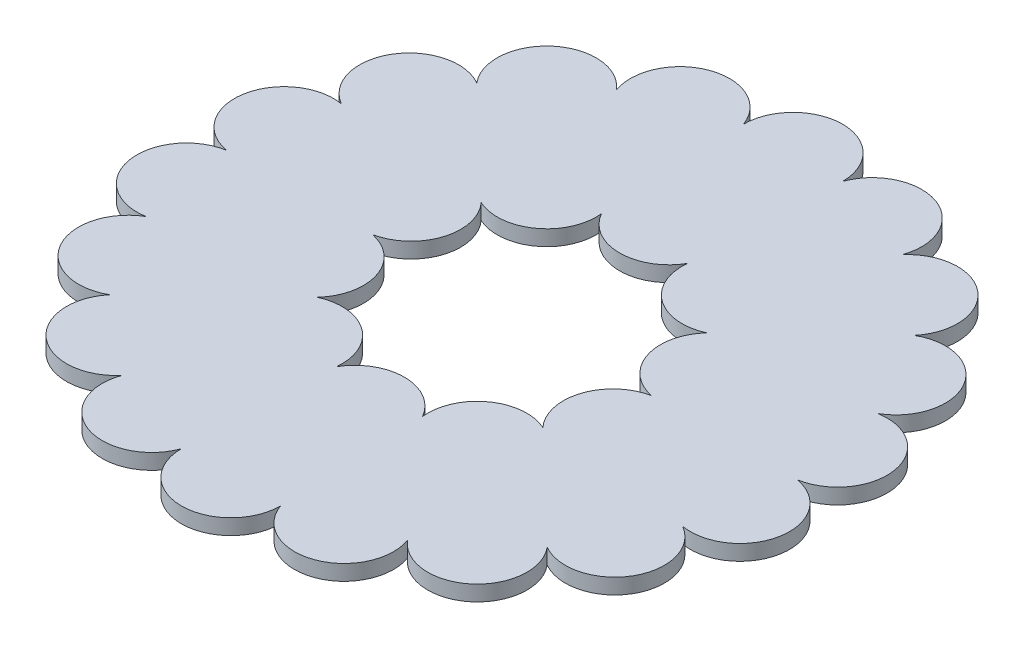
SolidWorks part; units mm, degrees
ref_plane "Front Plane" through (0, 0, 0) normal (0, 0, 1) x (1, 0, 0)
ref_plane "Top Plane" through (0, 0, 0) normal (0, 1, 0) x (1, 0, 0)
ref_plane "Right Plane" through (0, 0, 0) normal (1, 0, 0) x (0, 0, -1)
sketch "Sketch1" plane through (0, 0, 0) normal (0, 1, 0) x (1, 0, 0)
  circle A0 centre (0, 0) radius 64.4026
  circle A1 centre (0, 0) radius 115.2026
  point P8 (0, 0)
  dimension "D1" = 50.8
  dimension "D2" = 128.8051
extrude "Boss-Extrude1" add sketch "Sketch1" along normal blind 6.35
sketch "Sketch2" plane through (0, 6.35, 0) normal (0, 1, 0) x (1, 0, 0)
  circle A0 centre (0, 64.4026) radius 20.32
  circle A1 centre (0, 0) radius 64.4026 construction
  circle A2 centre (0, 115.2026) radius 20.32
  circle A3 centre (0, 0) radius 115.2026 construction
  circle A4 centre (37.8549, 52.1028) radius 20.32
  circle A5 centre (61.2505, 19.9015) radius 20.32
  circle A6 centre (61.2505, -19.9015) radius 20.32
  circle A7 centre (37.8549, -52.1028) radius 20.32
  circle A8 centre (0, -64.4026) radius 20.32
  circle A9 centre (-37.8549, -52.1028) radius 20.32
  circle A10 centre (-61.2505, -19.9015) radius 20.32
  circle A11 centre (-61.2505, 19.9015) radius 20.32
  circle A12 centre (-37.8549, 52.1028) radius 20.32
  circle A13 centre (39.4016, 108.255) radius 20.32
  circle A14 centre (74.0508, 88.2503) radius 20.32
  circle A15 centre (99.7683, 57.6013) radius 20.32
  circle A16 centre (113.4524, 20.0047) radius 20.32
  circle A17 centre (113.4524, -20.0047) radius 20.32
  circle A18 centre (99.7683, -57.6013) radius 20.32
  circle A19 centre (74.0508, -88.2503) radius 20.32
  circle A20 centre (39.4016, -108.255) radius 20.32
  circle A21 centre (0, -115.2026) radius 20.32
  circle A22 centre (-39.4016, -108.255) radius 20.32
  circle A23 centre (-74.0508, -88.2503) radius 20.32
  circle A24 centre (-99.7683, -57.6013) radius 20.32
  circle A25 centre (-113.4524, -20.0047) radius 20.32
  circle A26 centre (-113.4524, 20.0047) radius 20.32
  circle A27 centre (-99.7683, 57.6013) radius 20.32
  circle A28 centre (-74.0508, 88.2503) radius 20.32
  circle A29 centre (-39.4016, 108.255) radius 20.32
  point P28 (0, 0)
  point P63 (0, 0)
  dimension "D1" = 10
  dimension "D2" = 18
extrude "Boss-Extrude2" add sketch "Sketch2" against normal blind 6.35 contours A27 | A26 | A25 | A24 | A23 | A22 | A21 | A20 | A19 | A18 | A17 | A16 | A15 | A14 | A13 | A2 | A29 | A28 | A12 | A11 | A10 | A9 | A8 | A7 | A6 | A5 | A4 | A0
sketch "Sketch3" plane through (0, 6.35, 0) normal (0, 1, 0) x (1, 0, 0)
  point P0 (0, 0)
